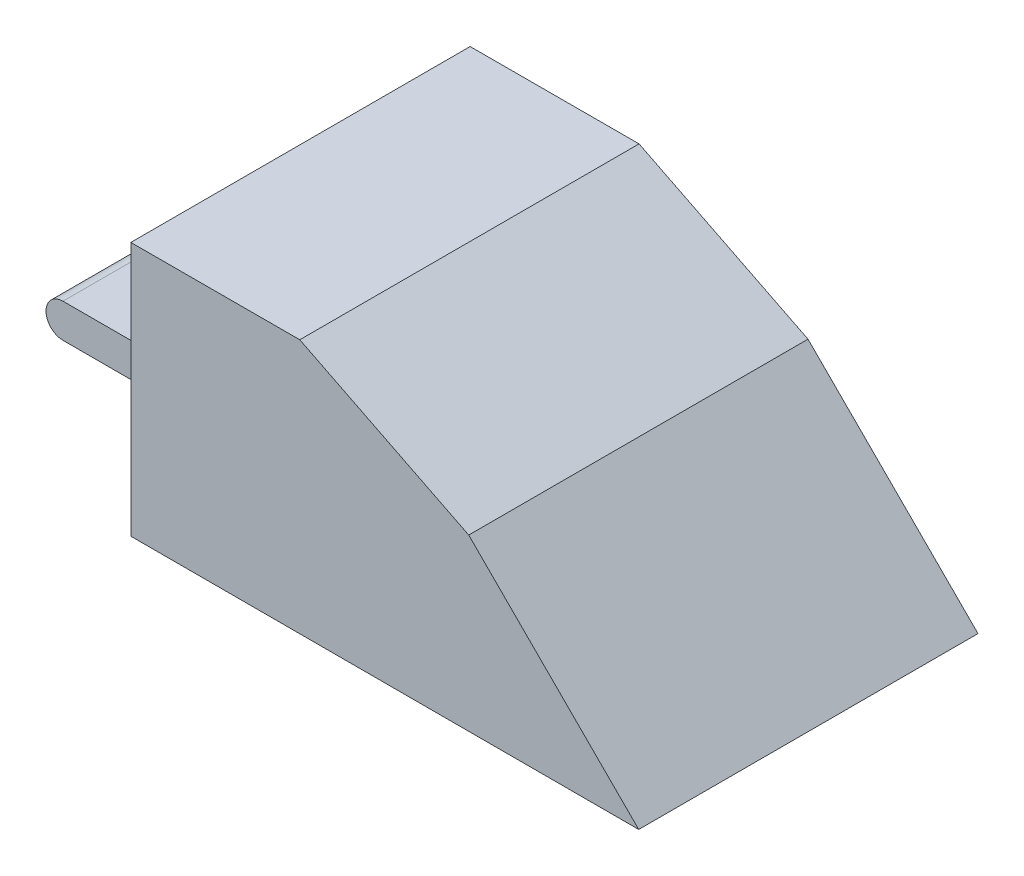
SolidWorks part; units mm, degrees
ref_plane "Front" through (0, 0, 0) normal (0, 0, 1) x (1, 0, 0)
ref_plane "Top" through (0, 0, 0) normal (0, 1, 0) x (1, 0, 0)
ref_plane "Right" through (0, 0, 0) normal (1, 0, 0) x (0, 0, -1)
sketch "草图1" plane through (0, 0, 0) normal (0, 1, 0) x (1, 0, 0)
  line L1 (-2, 10) -> (38, 10)
  line L2 (-2, 10) -> (-2, -10)
  line L3 (-2, -10) -> (38, -10)
  line L4 (38, 10) -> (38, -10)
  dimension "D1" = 40
  dimension "D2" = 38
  dimension "D3" = 20
  dimension "D4" = 10
extrude "凸台-拉伸1" add sketch "草图1" along normal blind 20
sketch "草图2" plane through (-2, 0, 0) normal (-1, 0, 0) x (0, 0, 1)
  line L0 (-10, 0) -> (10, 0) construction
  line L1 (-4, 0) -> (4, 0)
  line L2 (-4, 0) -> (-4, 4)
  line L3 (-4, 4) -> (4, 4)
  line L4 (4, 0) -> (4, 4)
  line L5 (0, 0) -> (0, 20) construction
  line L6 (-10, 20) -> (10, 20) construction
  dimension "D1" = 4
  dimension "D2" = 8
  dimension "D3" = 4
extrude "凸台-拉伸2" add sketch "草图2" along normal blind 10
sketch "草图12" plane through (0, 0, 4) normal (0, 0, 1) x (1, 0, 0)
  line L1 (-5, 2) -> (-18.4748, 2)
  line L3 (-5, 0) -> (-18.4748, 0)
  line L4 (-18.4748, 2) -> (-18.4748, 0)
  arc A0 (-5, 2) -> (-5, 0) centre (-5, 1) ccw
extrude "切除-拉伸8" cut sketch "草图12" against normal blind 20
sketch "草图13" plane through (0, 0, 4) normal (0, 0, 1) x (1, 0, 0)
  line L0 (-12, 2) -> (-12, 4) construction
  circle A0 centre (-12, 3) radius 1
extrude "凸台-拉伸5" add sketch "草图13" against normal blind 8
sketch "草图14" plane through (0, 0, 10) normal (0, 0, 1) x (1, 0, 0)
  line L3 (40.7368, 20.9474) -> (-2, 20)
  line L4 (-2, 20) -> (-2, 15)
  line L6 (17.9188, 10.0203) -> (7.9594, 15.0102)
  line L7 (17.9188, 10.0203) -> (27.9391, 0)
  line L8 (-2, 0) -> (38, 0) construction
  line L9 (27.9391, 0) -> (43.2758, 0)
  line L10 (43.2758, 0) -> (40.7368, 20.9474)
  line L12 (-2, 15) -> (7.9594, 15.0102)
extrude "切除-拉伸9" cut sketch "草图14" against normal blind 20
